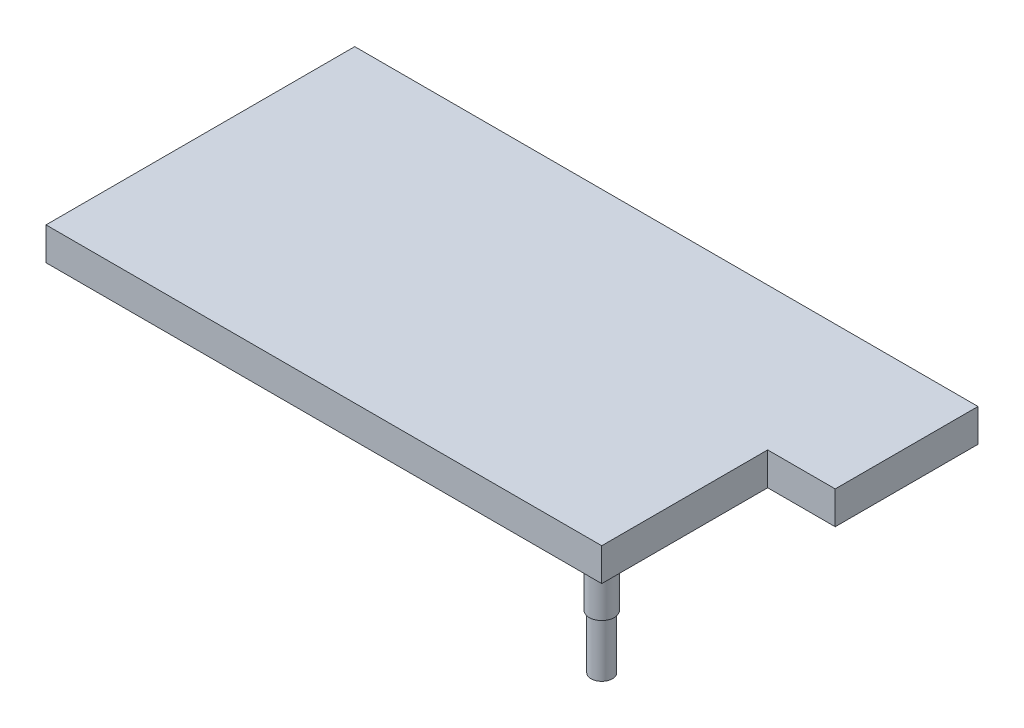
SolidWorks part; units mm, degrees
ref_plane "Front Plane" through (0, 0, 0) normal (0, 0, 1) x (1, 0, 0)
ref_plane "Top Plane" through (0, 0, 0) normal (0, 1, 0) x (1, 0, 0)
ref_plane "Right Plane" through (0, 0, 0) normal (1, 0, 0) x (0, 0, -1)
sketch "Sketch1" plane through (0, 0, 0) normal (0, 1, 0) x (1, 0, 0)
  line L2 (-914.4, 0) -> (-914.4, 508)
  line L3 (-914.4, 508) -> (0, 508)
  line L5 (0, 0) -> (-914.4, 0)
  line L6 (0, 0) -> (0, 508)
  dimension "D1" = 508
  dimension "D3" = 914.4
extrude "Boss-Extrude1" add sketch "Sketch1" along normal mid plane 3.175
sketch "Sketch2" plane through (0, -1.5875, 0) normal (0, -1, 0) x (1, 0, 0)
  line L0 (0, 0) -> (0, -508) construction
  line L1 (0, 0) -> (0, -508)
  line L2 (-863.6, -50.8) -> (-863.6, -457.2)
  line L3 (-863.6, -457.2) -> (-50.8, -457.2)
  line L4 (-50.8, -50.8) -> (-50.8, -457.2)
  line L5 (-50.8, -50.8) -> (-863.6, -50.8)
  line L6 (-914.4, -508) -> (0, -508)
  line L9 (0, -508) -> (0, 0)
  line L10 (0, 0) -> (-914.4, 0)
  line L11 (-914.4, 0) -> (-914.4, -508)
  line L12 (-914.4, -508) -> (0, -508)
  line L16 (0, 0) -> (-914.4, 0)
  line L17 (-914.4, 0) -> (-914.4, -508)
  dimension "D1" = 0
  dimension "D2" = 50.8
extrude "Boss-Extrude2" add sketch "Sketch2" along normal blind 50.8
sketch "Sketch3" plane through (0, -52.3875, 0) normal (0, -1, 0) x (1, 0, 0)
  line L0 (-50.8, -50.8) -> (0, -50.8) construction
  line L2 (-50.8, -50.8) -> (-50.8, 0) construction
  line L3 (0, 0) -> (-914.4, 0) construction
  line L4 (-50.8, -25.4) -> (-25.4, -25.4) construction
  line L5 (-25.4, -25.4) -> (-25.4, -50.8) construction
  line L6 (0, -508) -> (0, 0) construction
  circle A0 centre (-25.4, -25.4) radius 17.4625
  dimension "D1" = 34.925
extrude "Boss-Extrude3" add sketch "Sketch3" along normal blind 152.4
sketch "Sketch4" plane through (0, -52.3875, 0) normal (0, -1, 0) x (1, 0, 0)
  circle A0 centre (-25.4, -25.4) radius 20.6375
  circle A1 centre (-25.4, -25.4) radius 17.4625 construction
  circle A2 centre (-25.4, -25.4) radius 17.4625
  dimension "D1" = 41.275
extrude "Boss-Extrude4" add sketch "Sketch4" along normal blind 63.5 separate body
sketch "Sketch5" plane through (0, 0, 0) normal (1, 0, 0) x (0, 0, -1)
  line L0 (508, -52.3875) -> (0, -52.3875) construction
  line L1 (508, 1.5875) -> (273.05, 1.5875)
  line L2 (508, 1.5875) -> (508, -52.3875)
  line L3 (508, -52.3875) -> (273.05, -52.3875)
  line L4 (273.05, 1.5875) -> (273.05, -52.3875)
  dimension "D1" = 234.95
extrude "Boss-Extrude5" add sketch "Sketch5" along normal blind 111.125
